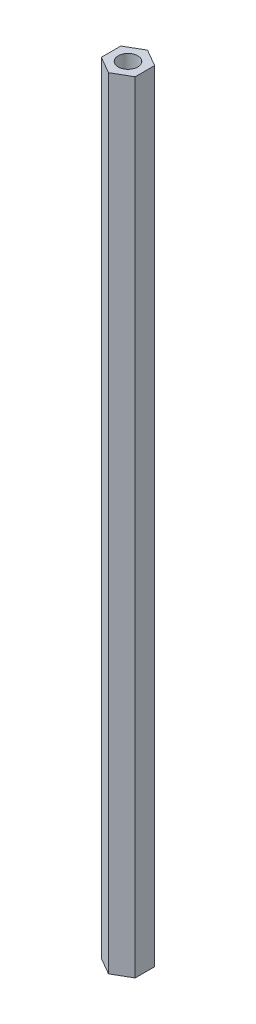
SolidWorks part; units mm, degrees
ref_plane "Face" through (0, 0, 0) normal (0, 0, 1) x (1, 0, 0)
ref_plane "Dessus" through (0, 0, 0) normal (0, 1, 0) x (1, 0, 0)
ref_plane "Droite" through (0, 0, 0) normal (1, 0, 0) x (0, 0, -1)
sketch "Esquisse1" plane through (0, 0, 0) normal (0, 1, 0) x (1, 0, 0)
  line L0 (0, 0) -> (0, 5.5688) construction
  line L1 (0, 5) -> (-4.3301, 2.5)
  line L2 (-4.3301, 2.5) -> (-4.3301, -2.5)
  line L3 (-4.3301, -2.5) -> (0, -5)
  line L4 (0, -5) -> (4.3301, -2.5)
  line L5 (4.3301, -2.5) -> (4.3301, 2.5)
  line L6 (4.3301, 2.5) -> (0, 5)
  circle A0 centre (0, 0) radius 4.3301 construction
  circle A1 centre (0, 0) radius 2.5
  dimension "D1" = 10
  dimension "D2" = 5
extrude "Extrusion1" add sketch "Esquisse1" along normal blind 200
